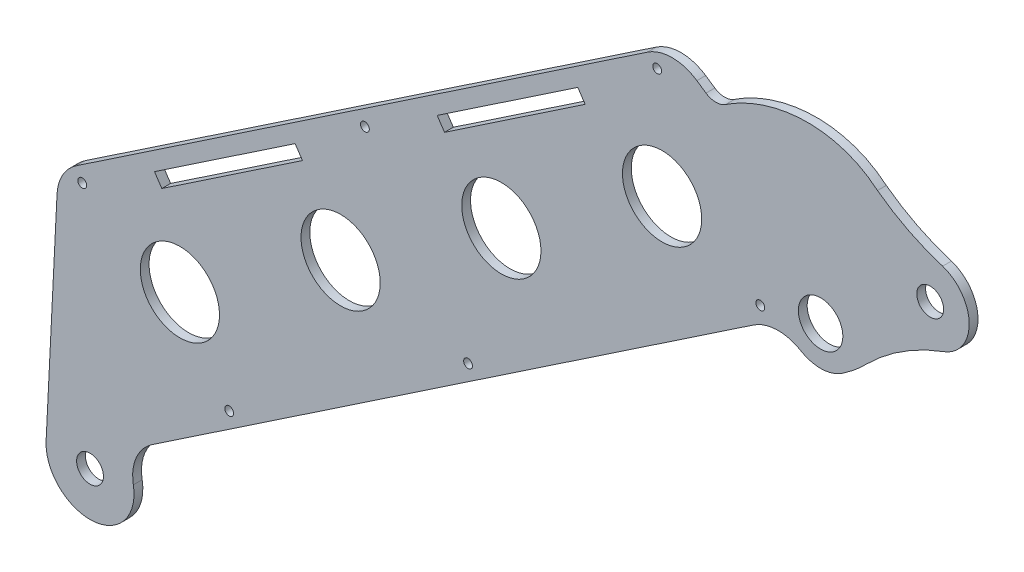
SolidWorks part; units mm, degrees
ref_plane "前视基准面" through (0, 0, 0) normal (0, 0, 1) x (1, 0, 0)
ref_plane "上视基准面" through (0, 0, 0) normal (0, 1, 0) x (1, 0, 0)
ref_plane "右视基准面" through (0, 0, 0) normal (1, 0, 0) x (0, 0, -1)
sketch "草图1" plane through (0, 0, 0) normal (0, 0, 1) x (1, 0, 0)
  line L0 (27.2208, 58.9518) -> (-80.6684, -13.5735) construction
  line L1 (44.8154, 53.8175) -> (59.8111, 27.8424) construction
  line L2 (33.7814, 60.1435) -> (26.1114, 65.3367)
  line L3 (26.1114, 65.3367) -> (-113.4149, -28.4557)
  line L4 (-113.4149, -28.4557) -> (-116.1723, -83.7351)
  line L5 (-98.943, -76.5646) -> (51.5624, 24.6083)
  line L6 (135.9432, 79.0199) -> (-138.5048, -105.4696) construction
  line L7 (-97.8731, -78.1562) -> (-98.943, -76.5646)
  line L8 (156.318, 0) -> (-175.4101, 0) construction
  line L9 (0, 169.76) -> (0, -134.3458) construction
  line L10 (0, 0) -> (-51.3159, 76.3379) construction
  circle A0 centre (-106.1723, -83.7351) radius 3.05
  circle A1 centre (59.8111, 27.8424) radius 5.05
  circle A4 centre (44.8154, 53.8175) radius 1 construction
  arc A8 (-116.1723, -83.7351) -> (-97.8731, -78.1562) centre (-106.1723, -83.7351) ccw
  arc A10 (51.5624, 24.6083) -> (64.7535, 20.4889) centre (59.8111, 27.8424) ccw
  arc A11 (87.7637, 36.2624) -> (70.0622, 24.8877) centre (104.4521, -9.1695) ccw
  arc A12 (87.7637, 36.2624) -> (87.5426, 52.9736) centre (84.7087, 44.579) ccw
  arc A13 (72.739, 60.4502) -> (87.5426, 52.9736) centre (101.6377, 99.2758) ccw
  arc A14 (33.7814, 60.1435) -> (38.2444, 60.1285) centre (36.024, 63.4557) ccw
  spline S0 degree 3 poles (64.7535, 20.4889) (66.6385, 21.7559) (68.4267, 23.2365) (70.0622, 24.8877) knots 0.026109 0.026109 0.026109 0.026109 0.97364 0.97364 0.97364 0.97364
  spline S1 degree 3 poles (72.739, 60.4502) (71.671, 61.3522) (67.6967, 64.1093) (55.7838, 67.5664) (44.3815, 64.2241) (38.2444, 60.1285) knots 0.009949 0.009949 0.009949 0.009949 0.121591 0.393982 0.990068 0.990068 0.990068 0.990068
  dimension "D1" = 10.1
  dimension "D3" = 6.1
  dimension "D4" = 200
  dimension "D6" = 10
  dimension "D7" = 3.8357
  dimension "D9" = 2
  dimension "D10" = 86.088
  dimension "D11" = 29.9929
  dimension "D12" = 126.765
  dimension "D2" = 10.261
  dimension "D5" = 44
  dimension "D8" = 48
  dimension "D14" = 110
extrude "凸台-拉伸1" add sketch "草图1" along normal blind 2
sketch "草图2" plane through (0, 0, 0) normal (0, 0, -1) x (-1, 0, 0)
  circle A0 centre (-84.7087, 44.579) radius 3.05
  dimension "D1" = 6.1
extrude "切除-拉伸1" cut sketch "草图2" against normal through all
fillet "圆角1" radius 10 1 edges at (51.5624, 24.6083, 1)
fillet "圆角2" radius 10 2 edges at (26.1114, 65.3367, 1) (-113.4149, -28.4557, 1)
sketch "草图4" plane through (0, 0, 2) normal (0, 0, 1) x (1, 0, 0)
  line L0 (-44.3718, 17.9565) -> (-17.5932, -21.8795) construction
  line L3 (20.5123, 61.5729) -> (-109.2558, -25.6599) construction
  line L4 (-98.943, -76.5646) -> (44.5989, 19.9273) construction
  line L5 (-151.5788, -83.0289) -> (97.9432, 84.705) construction
  circle A0 centre (-49.2406, -14.235) radius 9
  circle A1 centre (-12.7243, 10.312) radius 9
  circle A2 centre (23.792, 34.8591) radius 9
  circle A3 centre (-85.757, -38.782) radius 9
  point P4 (-30.9825, -1.9615)
  dimension "D3" = 22
  dimension "D4" = 18
  dimension "D5" = 22
  dimension "D6" = 18
  dimension "D7" = 18
  dimension "D8" = 18
  dimension "D9" = 44
  dimension "D10" = 44
  dimension "D1" = 90
  dimension "D2" = 90
extrude "切除-拉伸3" cut sketch "草图4" against normal blind 10
fillet "圆角3" radius 10 1 edges at (-98.943, -76.5646, 1)
sketch "草图5" plane through (0, 0, 0) normal (0, 0, -1) x (-1, 0, 0)
  line L0 (-45.2479, 74.5859) -> (139.2499, -49.4374) construction
  line L1 (-20.5123, 61.5729) -> (109.2558, -25.6599) construction
  line L2 (-51.7196, 28.3288) -> (99.7042, -73.4614) construction
  line L3 (92.0595, -71.9373) -> (-44.5989, 19.9273) construction
  line L4 (-22.6746, 59.4116) -> (-46.1058, 24.5551) construction
  line L5 (43.7188, 14.7806) -> (20.2875, -20.0759) construction
  line L6 (107.9441, -28.3929) -> (84.5128, -63.2494) construction
  circle A0 centre (-22.6746, 59.4116) radius 1
  circle A1 centre (43.7188, 14.7806) radius 1
  circle A2 centre (107.9441, -28.3929) radius 1
  circle A3 centre (-46.1058, 24.5551) radius 1
  circle A4 centre (20.2875, -20.0759) radius 1
  circle A5 centre (84.5128, -63.2494) radius 1 construction
  circle A6 centre (74.5538, -56.5548) radius 1
  point P11 (23.9923, -22.5663)
  dimension "D2" = 2
  dimension "D3" = 80
  dimension "D6" = 2
  dimension "D7" = 2
  dimension "D8" = 12
  dimension "D1" = 3
  dimension "D4" = 3
  dimension "D5" = 90
extrude "切除-拉伸4" cut sketch "草图5" against normal blind 10
sketch "草图6" plane through (0, 0, 2) normal (0, 0, 1) x (1, 0, 0)
  line L0 (-90.6916, -19.2053) -> (-58.7398, 2.2733) construction
  line L1 (-91.5284, -17.9604) -> (-59.5766, 3.5182)
  line L2 (-89.8547, -20.4502) -> (-57.9029, 1.0285)
  line L3 (20.5123, 61.5729) -> (-109.2558, -25.6599) construction
  line L4 (-107.9441, -28.3929) -> (-43.7188, 14.7806) construction
  line L5 (-75.8314, -6.8061) -> (-70.2674, -15.0833) construction
  line L6 (-89.8547, -20.4502) -> (-91.5284, -17.9604)
  line L7 (-57.9029, 1.0285) -> (-59.5766, 3.5182)
  line L8 (-43.7188, 14.7806) -> (-34.6661, 1.3139) construction
  line L9 (5.4856, 45.4469) -> (-26.4662, 23.9683) construction
  line L10 (4.6487, 46.6918) -> (-27.3031, 25.2131)
  line L11 (6.3224, 44.202) -> (-25.6294, 22.7234)
  line L12 (-27.3031, 25.2131) -> (-25.6294, 22.7234)
  line L13 (4.6487, 46.6918) -> (6.3224, 44.202)
  arc A0 (-91.5284, -17.9604) -> (-89.8547, -20.4502) centre (-90.6916, -19.2053) ccw
  arc A1 (-57.9029, 1.0285) -> (-59.5766, 3.5182) centre (-58.7398, 2.2733) ccw
  arc A2 (4.6487, 46.6918) -> (6.3224, 44.202) centre (5.4856, 45.4469) cw
  arc A3 (-25.6294, 22.7234) -> (-27.3031, 25.2131) centre (-26.4662, 23.9683) cw
  point P2 (-74.7157, -8.466)
  point P9 (-57.4949, 3.1102)
  point P22 (-10.4903, 34.7076)
  dimension "D3" = 40
  dimension "D1" = 5
  dimension "D2" = 3
  dimension "D4" = 90
extrude "切除-拉伸5" cut sketch "草图6" against normal blind 10 contours L13 L10 L12 L11 | L2 L7 L1 L6
